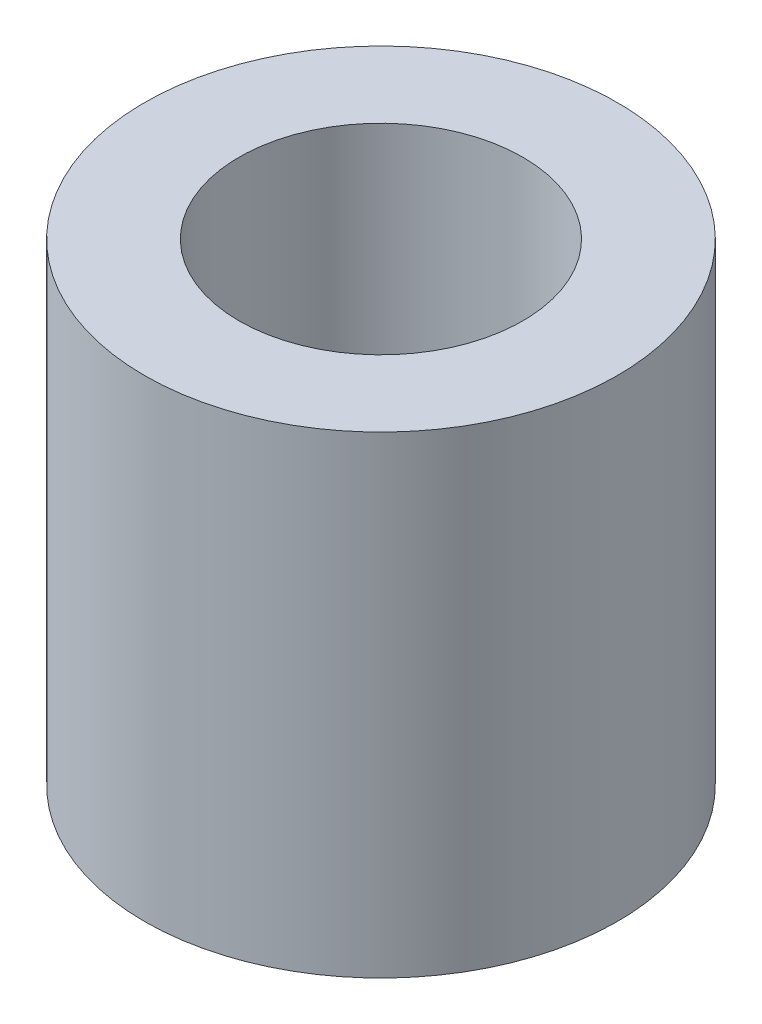
SolidWorks part; units mm, degrees
ref_plane "Front Plane" through (0, 0, 0) normal (0, 0, 1) x (1, 0, 0)
ref_plane "Top Plane" through (0, 0, 0) normal (0, 1, 0) x (1, 0, 0)
ref_plane "Right Plane" through (0, 0, 0) normal (1, 0, 0) x (0, 0, -1)
sketch "Sketch1" plane through (0, 0, 0) normal (0, 1, 0) x (1, 0, 0)
  circle A0 centre (0, 0) radius 2.5
  circle A1 centre (0, 0) radius 1.5
extrude "Boss-Extrude1" add sketch "Sketch1" along normal blind 5
